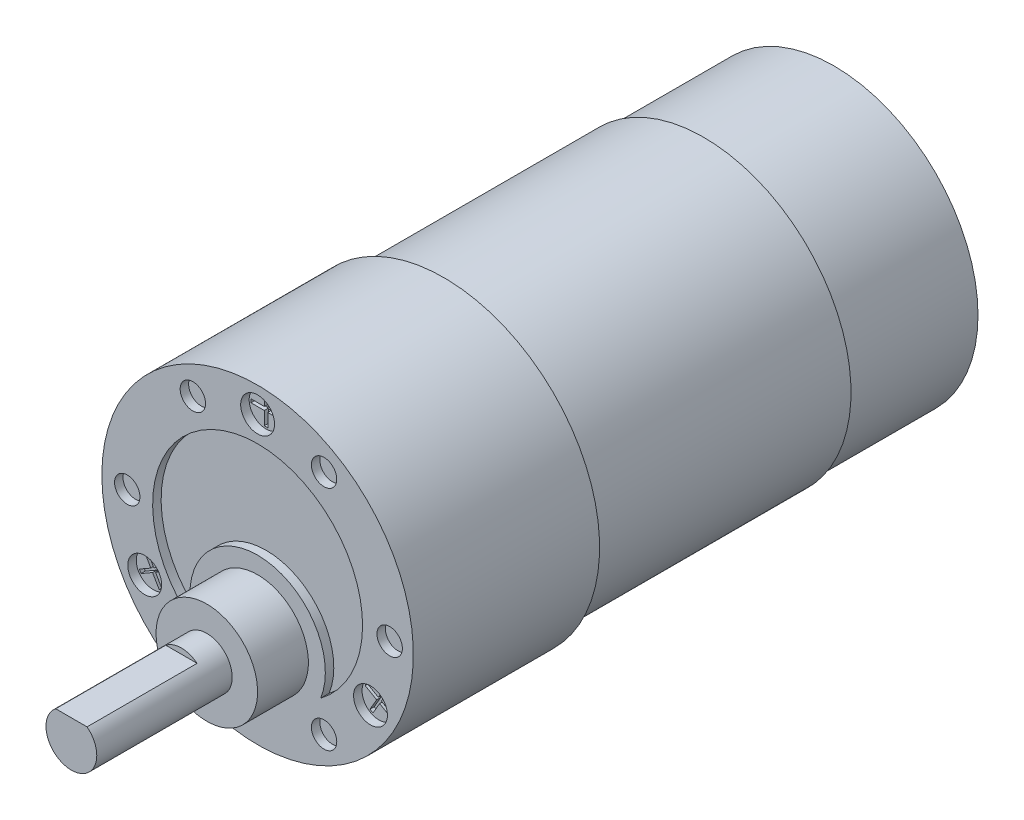
SolidWorks part; units mm, degrees
ref_plane "Front Plane" through (0, 0, 0) normal (0, 0, 1) x (1, 0, 0)
ref_plane "Top Plane" through (0, 0, 0) normal (0, 1, 0) x (1, 0, 0)
ref_plane "Right Plane" through (0, 0, 0) normal (1, 0, 0) x (0, 0, -1)
sketch "Sketch1" plane through (0, 0, 0) normal (0, 0, 1) x (1, 0, 0)
  circle A1 centre (0, 0) radius 3
  dimension "D1" = 6
extrude "Boss-Extrude1" add sketch "Sketch1" against normal blind 16
sketch "Sketch2" plane through (0, 0, 0) normal (0, 0, 1) x (1, 0, 0)
  line L0 (-1.8541, 2.3585) -> (1.8541, 2.3585)
  arc A2 (-1.8541, 2.3585) -> (1.8541, 2.3585) centre (0, 0) cw
  circle A3 centre (0, 0) radius 3 construction
  dimension "D1" = 3.7081
extrude "Cut-Extrude1" cut sketch "Sketch2" against normal blind 13
sketch "Sketch4" plane through (0, 0, -16) normal (0, 0, -1) x (-1, 0, 0)
  circle A0 centre (0, 0) radius 6
  dimension "D1" = 12
extrude "Boss-Extrude2" add sketch "Sketch4" along normal blind 6
sketch "Sketch5" plane through (0, 0, -22) normal (0, 0, -1) x (-1, 0, 0)
  line L0 (0, 0) -> (0, 7) construction
  circle A0 centre (0, 7) radius 18.4
  dimension "D2" = 36.8
  dimension "D1" = 7
extrude "Boss-Extrude3" add sketch "Sketch5" along normal blind 22
sketch "Sketch6" plane through (0, 0, -44) normal (0, 0, -1) x (-1, 0, 0)
  circle A0 centre (0, 7) radius 17.4
  dimension "D1" = 34.8
extrude "Boss-Extrude4" add sketch "Sketch6" along normal blind 30.7
sketch "Sketch7" plane through (0, 0, -74.7) normal (0, 0, -1) x (-1, 0, 0)
  circle A0 centre (0, 7) radius 17
  dimension "D1" = 34
extrude "Boss-Extrude5" add sketch "Sketch7" along normal blind 15.4
sketch "Sketch8" plane through (0, 0, -22) normal (0, 0, 1) x (1, 0, 0)
  line L0 (-18.4, 7) -> (-15.4, 7) construction
  line L1 (0, 7) -> (0, 25.4) construction
  circle A0 centre (0, 7) radius 18.4 construction
  circle A1 centre (0, 22.4) radius 2
  circle A2 centre (13.3368, -0.7) radius 2
  circle A3 centre (-13.3368, -0.7) radius 2
  circle A4 centre (-15.4, 7) radius 1.5
  circle A5 centre (-7.65, 20.4234) radius 1.5
  circle A6 centre (7.85, 20.4234) radius 1.5
  circle A7 centre (15.6, 7) radius 1.5
  circle A8 centre (7.85, -6.4234) radius 1.5
  circle A9 centre (-7.65, -6.4234) radius 1.5
  point P13 (0, 7)
  point P28 (0.1, 7)
  dimension "D1" = 4
  dimension "D5" = 3
  dimension "D2" = 3
  dimension "D4" = 3
  dimension "D7" = 15.5
  dimension "D3" = 3
  dimension "D6" = 6
extrude "Cut-Extrude2" cut sketch "Sketch8" against normal blind 1
sketch "Sketch9" plane through (0, 0, -22) normal (0, 0, 1) x (1, 0, 0)
  circle A2 centre (0, 0) radius 8
  arc A3 (7.4514, -2.9114) -> (-7.4514, -2.9114) centre (0, 0) ccw
  circle A5 centre (0, 7) radius 12.4
  arc A6 (7.4514, -2.9114) -> (-7.4514, -2.9114) centre (0, 7) ccw
  dimension "D1" = 2
  dimension "D2" = 6
extrude "Cut-Extrude3" cut sketch "Sketch9" against normal blind 1
sketch "Sketch10" plane through (0, 0, -23) normal (0, 0, 1) x (1, 0, 0)
  line L0 (0.1988, 22.6048) -> (1.7651, 22.6048)
  line L1 (0.1988, 24.1711) -> (-0.2109, 24.1711)
  line L2 (0.1988, 24.1711) -> (0.1988, 22.6048)
  line L3 (0.1988, 20.6289) -> (-0.2109, 20.6289)
  line L4 (-0.2109, 24.1711) -> (-0.2109, 22.6048)
  line L5 (13.4148, -0.9746) -> (12.6316, -2.331)
  line L6 (14.7712, -1.7577) -> (14.9761, -1.4029)
  line L7 (-1.7771, 22.6048) -> (-0.2109, 22.6048)
  line L8 (-1.7771, 22.6048) -> (-1.7771, 22.1952)
  line L9 (-1.7771, 22.1952) -> (-0.2109, 22.1952)
  line L10 (1.7651, 22.6048) -> (1.7651, 22.1952)
  line L11 (14.7712, -1.7577) -> (13.4148, -0.9746)
  line L12 (11.7036, 0.0134) -> (11.9084, 0.3682)
  line L14 (-0.2109, 22.1952) -> (-0.2109, 20.6289)
  line L16 (0.1988, 22.1952) -> (0.1988, 20.6289)
  line L17 (0.1988, 22.1952) -> (1.7651, 22.1952)
  line L18 (14.9761, -1.4029) -> (13.6196, -0.6198)
  line L19 (14.4028, 0.7366) -> (13.6196, -0.6198)
  line L20 (14.4028, 0.7366) -> (14.048, 0.9415)
  line L21 (14.048, 0.9415) -> (13.2648, -0.415)
  line L22 (12.6316, -2.331) -> (12.2768, -2.1262)
  line L23 (13.2648, -0.415) -> (11.9084, 0.3682)
  line L24 (13.06, -0.7698) -> (11.7036, 0.0134)
  line L25 (13.06, -0.7698) -> (12.2768, -2.1262)
  line L26 (-13.6136, -0.6302) -> (-14.3967, 0.7262)
  line L27 (-14.97, -1.4134) -> (-14.7652, -1.7682)
  line L28 (-14.97, -1.4134) -> (-13.6136, -0.6302)
  line L29 (-11.9024, 0.3577) -> (-11.6975, 0.0029)
  line L30 (-14.7652, -1.7682) -> (-13.4088, -0.985)
  line L31 (-12.6256, -2.3415) -> (-13.4088, -0.985)
  line L32 (-12.6256, -2.3415) -> (-12.2708, -2.1366)
  line L33 (-12.2708, -2.1366) -> (-13.054, -0.7802)
  line L34 (-14.3967, 0.7262) -> (-14.0419, 0.931)
  line L35 (-13.054, -0.7802) -> (-11.6975, 0.0029)
  line L36 (-13.2588, -0.4254) -> (-11.9024, 0.3577)
  line L37 (-13.2588, -0.4254) -> (-14.0419, 0.931)
  point P0 (0, 22.4)
  point P6 (0, 22.4)
  point P15 (13.3368, -0.7)
  point P22 (13.3368, -0.7)
  point P31 (-13.3368, -0.7)
  point P36 (-13.3368, -0.7)
  point P45 (0, 7)
  dimension "D1" = 3
extrude "Cut-Extrude4" cut sketch "Sketch10" against normal blind 0.5
